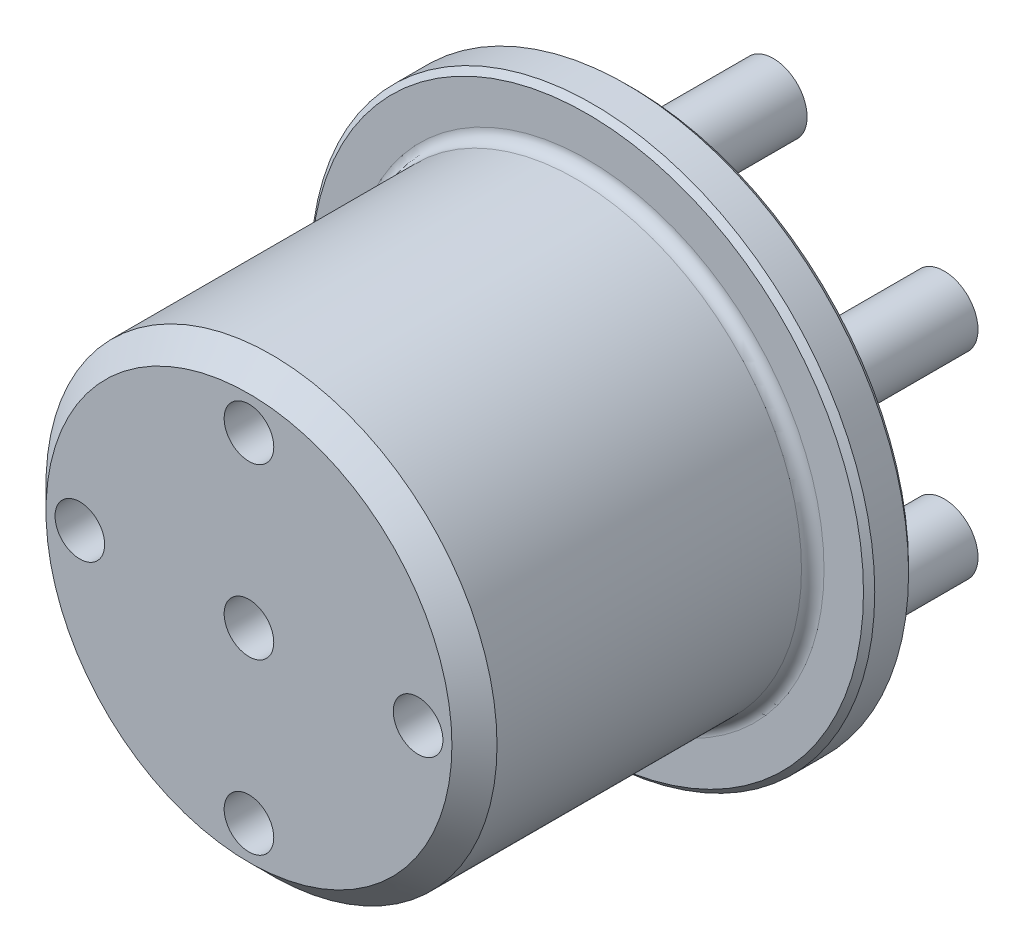
SolidWorks part; units mm, degrees
material "Polylactic Acid (PLA)"
ref_plane "Front Plane" through (0, 0, 0) normal (0, 0, 1) x (1, 0, 0)
ref_plane "Top Plane" through (0, 0, 0) normal (0, 1, 0) x (1, 0, 0)
ref_plane "Right Plane" through (0, 0, 0) normal (1, 0, 0) x (0, 0, -1)
sketch "Sketch1" plane through (0, 0, 0) normal (0, 0, 1) x (1, 0, 0)
  circle A0 centre (0, 0) radius 25
  circle A1 centre (0, 0) radius 15 construction
  dimension "D1" = 50
  dimension "D2" = 30
extrude "Boss-Extrude1" add sketch "Sketch1" against normal blind 4
sketch "Sketch2" plane through (0, 0, 0) normal (0, 0, 1) x (1, 0, 0)
  circle A0 centre (0, 0) radius 20
  dimension "D1" = 40
extrude "Boss-Extrude2" add sketch "Sketch2" along normal blind 30
fillet "Fillet1" radius 1 1 edges at (20, 0, 0)
sketch "Sketch3" plane through (0, 0, -4) normal (0, 0, -1) x (-1, 0, 0)
  circle A0 centre (0, 0) radius 10.2
  dimension "D1" = 20.4
extrude "Cut-Extrude1" cut sketch "Sketch3" against normal blind 5
sketch "Sketch4" plane through (0, 0, -4) normal (0, 0, -1) x (-1, 0, 0)
  circle A0 centre (0, 0) radius 17.5 construction
  circle A1 centre (0, 17.5) radius 3
  circle A2 centre (15.1554, 8.75) radius 3
  circle A3 centre (15.1554, -8.75) radius 3
  circle A4 centre (0, -17.5) radius 3
  circle A5 centre (-15.1554, -8.75) radius 3
  circle A6 centre (-15.1554, 8.75) radius 3
  circle A7 centre (0, 0) radius 10.2 construction
  point P17 (0, 0)
  dimension "D1" = 35
  dimension "D2" = 6
  dimension "D3" = 6
extrude "Boss-Extrude3" add sketch "Sketch4" along normal blind 12.5
sketch "Sketch7" plane through (0, 0, 30) normal (0, 0, 1) x (1, 0, 0)
  circle A0 centre (0, 0) radius 15 construction
  point P1 (0, 0)
  point P4 (0, 15)
  point P6 (15, 0)
  point P8 (0, -15)
  point P10 (-15, 0)
  dimension "D1" = 30
hole_wizard "Ø4.0mm Dowel Hole1" positions "Sketch7" profile "Sketch8" hole size "Ø4.0" standard "ISO"
sketch "Sketch8" plane through (0, 0, 30) normal (1, 0, 0) x (0, -1, 0)
  line L0 (0, 0) -> (0, 9.3219)
  line L1 (0, 9.3219) -> (2.2, 8)
  line L2 (2.2, 8) -> (2.2, 0)
  line L5 (2.2, 0) -> (0, 0)
  line L10 (0, 9.3219) -> (-2.2, 8) construction
  line L11 (0, -6.35) -> (0, 107.95) construction
  dimension "Hole Dia." = 4.4
  dimension "Hole Depth" = 8
  dimension "Drill Angle" = 118
fillet "Fillet2" radius 1 6 edges at (18.1554, 8.75, -4) (3, 17.5, -4) (-12.1554, 8.75, -4) (-12.1554, -8.75, -4) (3, -17.5, -4) (12.1554, -8.75, -4)
chamfer "Chamfer1" distance 0.5 angle 45 4 edges at (25, 0, -4) (-10.2, 0, -4) (-10.2, 0, 1) (25, 0, 0)
chamfer "Chamfer2" distance 2 angle 45 1 edges at (20, 0, 30)
